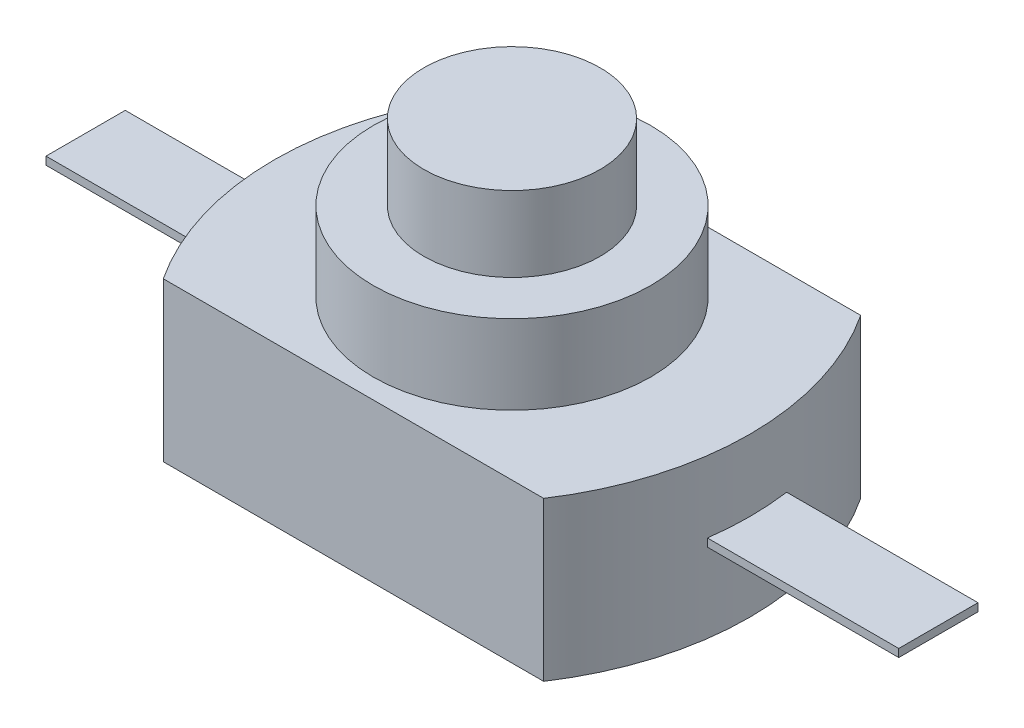
SolidWorks part; units mm, degrees
ref_plane "Front Plane" through (0, 0, 0) normal (0, 0, 1) x (1, 0, 0)
ref_plane "Top Plane" through (0, 0, 0) normal (0, 1, 0) x (1, 0, 0)
ref_plane "Right Plane" through (0, 0, 0) normal (1, 0, 0) x (0, 0, -1)
sketch "Sketch1" plane through (0, 0, 0) normal (0, 1, 0) x (1, 0, 0)
  line L0 (0, -4) -> (9.6, -4) construction
  line L1 (0, 0) -> (9.6, 0)
  line L2 (0, 0) -> (0, -8)
  line L3 (0, -8) -> (9.6, -8)
  line L4 (9.6, 0) -> (9.6, -8)
  line L5 (9.6, -4) -> (10.8, -4) construction
  line L6 (0, -4) -> (-1.2, -4) construction
  line L7 (4.8, 0) -> (4.8, -8) construction
  arc A0 (0, 0) -> (0, -8) centre (6.0667, -4) ccw
  arc A1 (9.6, 0) -> (9.6, -8) centre (3.5333, -4) cw
  dimension "D1" = 8
  dimension "D2" = 12
  dimension "D3" = 9.6
extrude "Boss-Extrude1" add sketch "Sketch1" along normal blind 4 contours L4 L1 L2 L3 | L2 A0 | A1 L4
sketch "Sketch2" plane through (0, 4, 0) normal (0, 1, 0) x (1, 0, 0)
  line L0 (4.8, 0) -> (4.8, -8) construction
  line L1 (0, 0) -> (9.6, 0) construction
  line L2 (0, -8) -> (9.6, -8) construction
  circle A0 centre (4.8, -4) radius 3.5
  dimension "D1" = 7
extrude "Boss-Extrude2" add sketch "Sketch2" along normal blind 2
sketch "Sketch3" plane through (0, 6, 0) normal (0, 1, 0) x (1, 0, 0)
  circle A0 centre (4.8, -4) radius 2.225
  dimension "D1" = 4.45
extrude "Boss-Extrude3" add sketch "Sketch3" along normal blind 1.9
sketch "Sketch4" plane through (0, 4, 0) normal (0, 1, 0) x (1, 0, 0)
  line L0 (-1.2, -4) -> (10.8, -4) construction
  line L1 (4.8, -4) -> (4.8, -2.0234) construction
  line L2 (-0.868, -3) -> (-5.96, -3)
  line L3 (-0.868, -3) -> (-0.868, -5)
  line L4 (-0.868, -5) -> (-5.96, -5)
  line L5 (-5.96, -3) -> (-5.96, -5)
  line L6 (10.468, -5) -> (15.56, -5)
  line L7 (15.56, -3) -> (15.56, -5)
  line L8 (10.468, -3) -> (15.56, -3)
  line L9 (10.468, -3) -> (10.468, -5)
  arc A0 (0, 0) -> (0, -8) centre (6.0667, -4) ccw construction
  arc A1 (9.6, -8) -> (9.6, 0) centre (3.5333, -4) ccw construction
  point P12 (-0.868, -4)
  dimension "D1" = 2
extrude "Boss-Extrude4" add sketch "Sketch4" along normal blind 0.2 from offset 2
